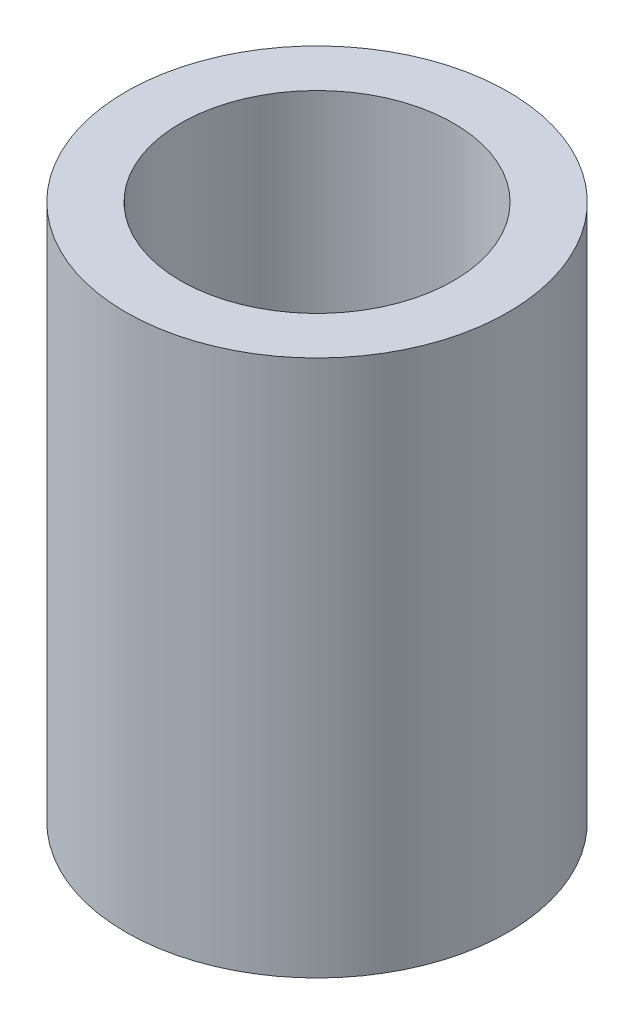
SolidWorks part; units mm, degrees
ref_plane "Front Plane" through (0, 0, 0) normal (0, 0, 1) x (1, 0, 0)
ref_plane "Top Plane" through (0, 0, 0) normal (0, 1, 0) x (1, 0, 0)
ref_plane "Right Plane" through (0, 0, 0) normal (1, 0, 0) x (0, 0, -1)
sketch "Sketch1" plane through (0, 0, 0) normal (0, 1, 0) x (1, 0, 0)
  circle A0 centre (0, 0) radius 2.1
  circle A1 centre (0, 0) radius 1.5
  dimension "D1" = 3
  dimension "D2" = 4.2
extrude "Boss-Extrude1" add sketch "Sketch1" along normal blind 5.9
